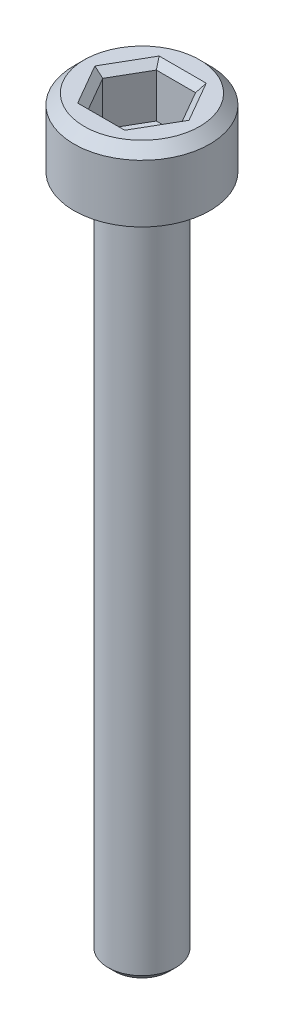
SolidWorks part; units mm, degrees
ref_plane "Front Plane" through (0, 0, 0) normal (0, 0, 1) x (1, 0, 0)
ref_plane "Top Plane" through (0, 0, 0) normal (0, 1, 0) x (1, 0, 0)
ref_plane "Right Plane" through (0, 0, 0) normal (1, 0, 0) x (0, 0, -1)
sketch "Sketch1" plane through (0, 0, 0) normal (0, 1, 0) x (1, 0, 0)
  circle A0 centre (0, 0) radius 2
  dimension "D1" = 4
extrude "Boss-Extrude1" add sketch "Sketch1" along normal blind 2
chamfer "Chamfer1" distance 0.3 angle 45 1 edges at (0, 2, 2)
sketch "Sketch2" plane through (0, 2, 0) normal (0, 1, 0) x (1, 0, 0)
  line L1 (1.1547, 0) -> (0.5774, 1)
  line L2 (0.5774, 1) -> (-0.5774, 1)
  line L3 (-0.5774, 1) -> (-1.1547, 0)
  line L4 (-1.1547, 0) -> (-0.5774, -1)
  line L5 (-0.5774, -1) -> (0.5774, -1)
  line L6 (0.5774, -1) -> (1.1547, 0)
  circle A0 centre (0, 0) radius 1 construction
  dimension "D1" = 2
extrude "Cut-Extrude1" cut sketch "Sketch2" against normal blind 1.5
chamfer "Chamfer2" distance 0.2 angle 45 6 edges at (0.866, 2, -0.5) (0.866, 2, 0.5) (0, 2, 1) (-0.866, 2, 0.5) (-0.866, 2, -0.5) (0, 2, -1)
sketch "Sketch3" plane through (0, 0, 0) normal (0, -1, 0) x (1, 0, 0)
  circle A0 centre (0, 0) radius 1
  dimension "D1" = 2
extrude "Boss-Extrude2" add sketch "Sketch3" along normal blind 20
chamfer "Chamfer3" distance 0.2 angle 45 1 edges at (0, -20, -1)
